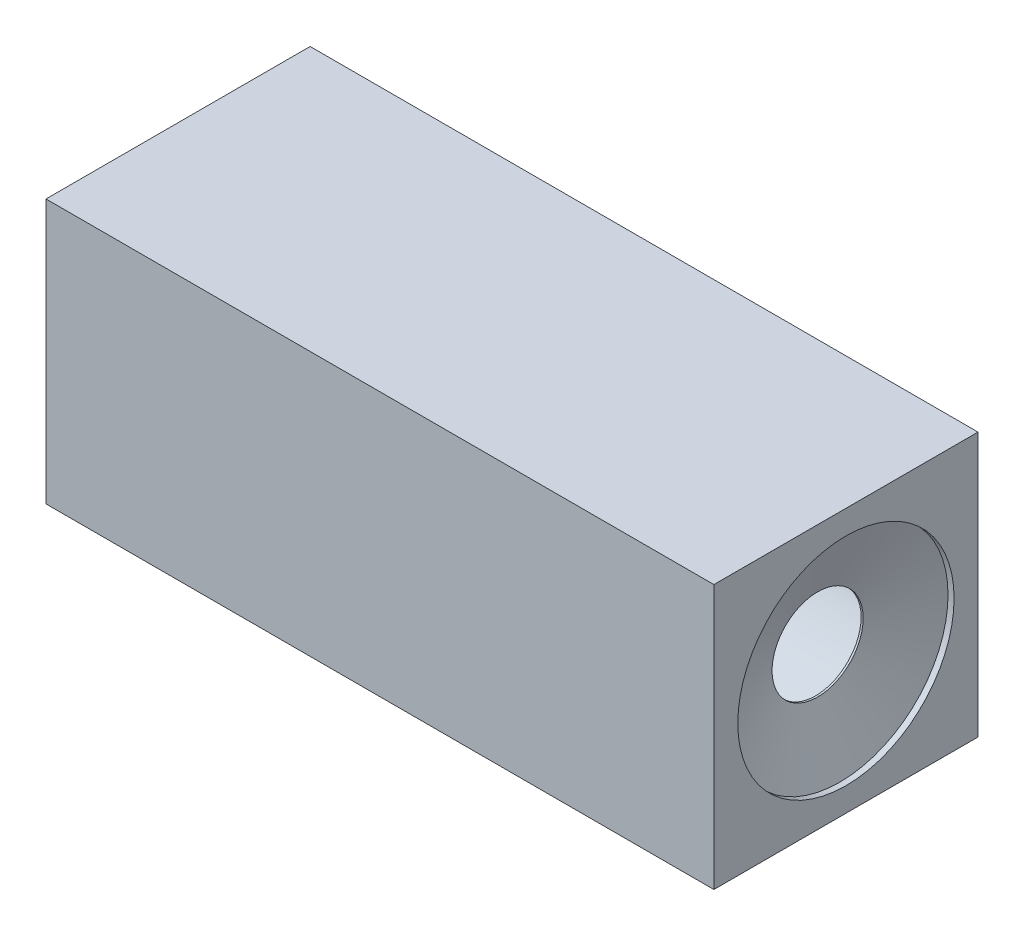
SolidWorks part; units mm, degrees
ref_plane "前视" through (0, 0, 0) normal (0, 0, 1) x (1, 0, 0)
ref_plane "上视" through (0, 0, 0) normal (0, 1, 0) x (1, 0, 0)
ref_plane "右视" through (0, 0, 0) normal (1, 0, 0) x (0, 0, -1)
sketch "草图1" plane through (0, 0, 0) normal (1, 0, 0) x (0, 0, -1)
  line L1 (-65.25, 65.25) -> (65.25, 65.25)
  line L2 (-65.25, 65.25) -> (-65.25, -65.25)
  line L3 (-65.25, -65.25) -> (65.25, -65.25)
  line L4 (65.25, 65.25) -> (65.25, -65.25)
  line L5 (-65.25, 65.25) -> (65.25, -65.25) construction
  line L6 (-65.25, -65.25) -> (65.25, 65.25) construction
  point P0 (0, 0)
extrude "凸台-拉伸1" add sketch "草图1" along normal blind 330
sketch "草图8" plane through (0, 0, 0) normal (-1, 0, 0) x (0, 0, 1)
  circle A0 centre (0, 0) radius 56.25
extrude "切除-拉伸2" cut sketch "草图8" against normal blind 315
ref_plane "基准面1" through (0, 0, 0) normal (0, 0, -1) x (-1, 0, 0)
sketch "草图26" plane through (0, 0, 0) normal (0, 0, -1) x (-1, 0, 0)
  line L0 (-315, 0) -> (-315, 22.5)
  line L1 (-315, -56.25) -> (-315, 56.25) construction
  line L2 (-315, 22.5) -> (-316, 22.5)
  line L3 (-330, 53.4393) -> (-327, 53.4393)
  line L4 (-330, -65.25) -> (-330, 65.25) construction
  line L5 (-327, 53.4393) -> (-316, 22.5)
  line L6 (-315, 0) -> (-330, 0)
  line L7 (-330, 0) -> (-330, 53.4393)
  dimension "D1" = 22.5
  dimension "D2" = 1
  dimension "D3" = 3
revolve "切除-旋转3" cut sketch "草图26" angle 360 about axis through (315, 0, 0) along (-1, 0, 0)
